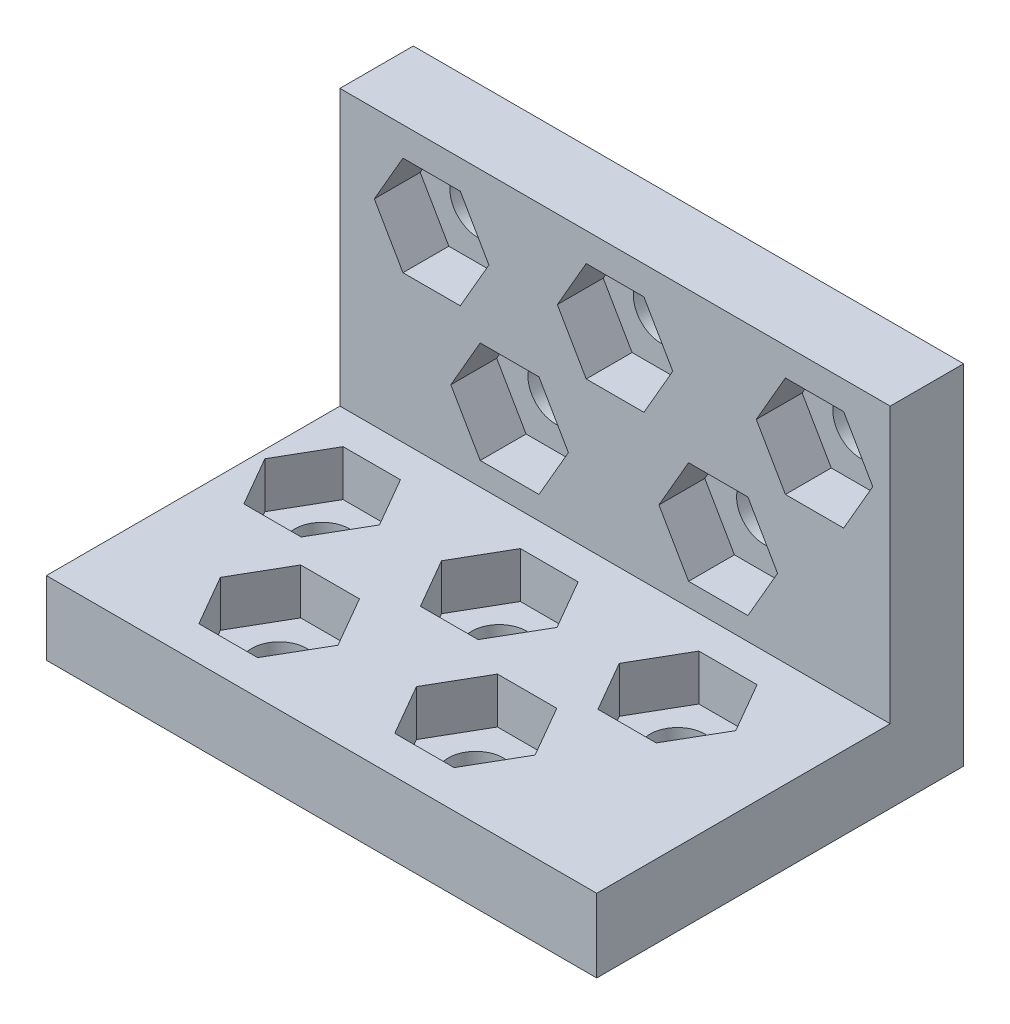
SolidWorks part; units mm, degrees
ref_plane "Front Plane" through (0, 0, 0) normal (0, 0, 1) x (1, 0, 0)
ref_plane "Top Plane" through (0, 0, 0) normal (0, 1, 0) x (1, 0, 0)
ref_plane "Right Plane" through (0, 0, 0) normal (1, 0, 0) x (0, 0, -1)
sketch "Sketch1" plane through (0, 0, 0) normal (0, 1, 0) x (1, 0, 0)
  line L1 (-15, 10) -> (15, 10)
  line L2 (-15, 10) -> (-15, -10)
  line L3 (-15, -10) -> (15, -10)
  line L4 (15, 10) -> (15, -10)
  line L5 (-15, 10) -> (15, -10) construction
  line L6 (-15, -10) -> (15, 10) construction
  point P0 (0, 0)
  dimension "D1" = 30
  dimension "D2" = 20
extrude "Boss-Extrude1" add sketch "Sketch1" along normal blind 4
sketch "Sketch2" plane through (0, 4, 0) normal (0, 1, 0) x (1, 0, 0)
  line L0 (15, -10) -> (15, 10) construction
  line L1 (-15, 10) -> (15, 10)
  line L2 (-15, 10) -> (-15, 6)
  line L3 (-15, 6) -> (15, 6)
  line L4 (15, 10) -> (15, 6)
  dimension "D1" = 4
extrude "Boss-Extrude2" add sketch "Sketch2" along normal blind 15
sketch "Sketch3" plane through (0, 0, -6) normal (0, 0, 1) x (1, 0, 0)
  line L0 (-15, 4) -> (15, 4) construction
  line L1 (-8.4383, 12.0162) -> (-6.8765, 14.7212)
  line L2 (-6.8765, 14.7212) -> (-8.4383, 17.4262)
  line L3 (-8.4383, 17.4262) -> (-11.5617, 17.4262)
  line L4 (-11.5617, 17.4262) -> (-13.1235, 14.7212)
  line L5 (-13.1235, 14.7212) -> (-11.5617, 12.0162)
  line L6 (-11.5617, 12.0162) -> (-8.4383, 12.0162)
  line L31 (-15, 19) -> (-15, 4) construction
  line L51 (1.5733, 11.993) -> (3.1466, 14.718)
  line L52 (3.1466, 14.718) -> (1.5733, 17.443)
  line L53 (1.5733, 17.443) -> (-1.5733, 17.443)
  line L54 (-1.5733, 17.443) -> (-3.1466, 14.718)
  line L55 (-3.1466, 14.718) -> (-1.5733, 11.993)
  line L56 (-1.5733, 11.993) -> (1.5733, 11.993)
  line L57 (12.4612, 11.9712) -> (14.049, 14.7212)
  line L58 (14.049, 14.7212) -> (12.4612, 17.4712)
  line L59 (12.4612, 17.4712) -> (9.2858, 17.4712)
  line L60 (9.2858, 17.4712) -> (7.6981, 14.7212)
  line L61 (7.6981, 14.7212) -> (9.2858, 11.9712)
  line L62 (9.2858, 11.9712) -> (12.4612, 11.9712)
  line L63 (-4.1471, 5.2564) -> (-2.5449, 8.0314)
  line L64 (-2.5449, 8.0314) -> (-4.1471, 10.8064)
  line L65 (-4.1471, 10.8064) -> (-7.3514, 10.8064)
  line L66 (-7.3514, 10.8064) -> (-8.9535, 8.0314)
  line L67 (-8.9535, 8.0314) -> (-7.3514, 5.2564)
  line L68 (-7.3514, 5.2564) -> (-4.1471, 5.2564)
  line L69 (7.2408, 5.2314) -> (8.8574, 8.0314)
  line L70 (8.8574, 8.0314) -> (7.2408, 10.8314)
  line L71 (7.2408, 10.8314) -> (4.0077, 10.8314)
  line L72 (4.0077, 10.8314) -> (2.3911, 8.0314)
  line L73 (2.3911, 8.0314) -> (4.0077, 5.2314)
  line L74 (4.0077, 5.2314) -> (7.2408, 5.2314)
  circle A0 centre (-10, 14.7212) radius 2.705 construction
  circle A1 centre (0, 14.718) radius 2.725 construction
  circle A2 centre (10.8735, 14.7212) radius 2.75 construction
  circle A3 centre (-5.7492, 8.0314) radius 2.775 construction
  circle A4 centre (5.6242, 8.0314) radius 2.8 construction
  dimension "D4" = 5.5
  dimension "D2" = 5
  dimension "D3" = 5.45
  dimension "D1" = 5.41
  dimension "D5" = 5.55
  dimension "D6" = 5.6
extrude "Cut-Extrude1" cut sketch "Sketch3" against normal blind 2.5
sketch "Sketch4" plane through (0, 0, -8.5) normal (0, 0, 1) x (1, 0, 0)
  circle A0 centre (-10, 14.7212) radius 1.5
  circle A1 centre (0, 14.718) radius 1.5
  circle A2 centre (10.8735, 14.7212) radius 1.5
  circle A3 centre (5.6242, 8.0314) radius 1.5
  circle A4 centre (-5.7492, 8.0314) radius 1.5
  dimension "D1" = 3
  dimension "D2" = 3
  dimension "D3" = 3
  dimension "D4" = 3
  dimension "D5" = 3
extrude "Cut-Extrude2" cut sketch "Sketch4" against normal through all both and the other way through all
sketch "Sketch5" plane through (0, 4, 0) normal (0, 1, 0) x (1, 0, 0)
  line L1 (-9.8742, -1.2364) -> (-8.3125, 1.4686)
  line L2 (-8.3125, 1.4686) -> (-9.8742, 4.1736)
  line L3 (-9.8742, 4.1736) -> (-12.9977, 4.1736)
  line L4 (-12.9977, 4.1736) -> (-14.5594, 1.4686)
  line L5 (-14.5594, 1.4686) -> (-12.9977, -1.2364)
  line L6 (-12.9977, -1.2364) -> (-9.8742, -1.2364)
  line L7 (-0.2077, -1.2564) -> (1.3655, 1.4686)
  line L8 (1.3655, 1.4686) -> (-0.2077, 4.1936)
  line L9 (-0.2077, 4.1936) -> (-3.3543, 4.1936)
  line L10 (-3.3543, 4.1936) -> (-4.9276, 1.4686)
  line L11 (-4.9276, 1.4686) -> (-3.3543, -1.2564)
  line L12 (-3.3543, -1.2564) -> (-0.2077, -1.2564)
  line L13 (9.5241, -1.2814) -> (11.1119, 1.4686)
  line L14 (11.1119, 1.4686) -> (9.5241, 4.2186)
  line L15 (9.5241, 4.2186) -> (6.3487, 4.2186)
  line L16 (6.3487, 4.2186) -> (4.761, 1.4686)
  line L17 (4.761, 1.4686) -> (6.3487, -1.2814)
  line L18 (6.3487, -1.2814) -> (9.5241, -1.2814)
  line L19 (-5.3657, -8.118) -> (-3.7635, -5.343)
  line L20 (-3.7635, -5.343) -> (-5.3657, -2.568)
  line L21 (-5.3657, -2.568) -> (-8.57, -2.568)
  line L22 (-8.57, -2.568) -> (-10.1721, -5.343)
  line L23 (-10.1721, -5.343) -> (-8.57, -8.118)
  line L24 (-8.57, -8.118) -> (-5.3657, -8.118)
  line L25 (5.1786, -7.9556) -> (6.7952, -5.1556)
  line L26 (6.7952, -5.1556) -> (5.1786, -2.3556)
  line L27 (5.1786, -2.3556) -> (1.9454, -2.3556)
  line L28 (1.9454, -2.3556) -> (0.3289, -5.1556)
  line L29 (0.3289, -5.1556) -> (1.9454, -7.9556)
  line L30 (1.9454, -7.9556) -> (5.1786, -7.9556)
  circle A0 centre (-11.436, 1.4686) radius 2.705 construction
  circle A1 centre (-1.781, 1.4686) radius 2.725 construction
  circle A2 centre (7.9364, 1.4686) radius 2.75 construction
  circle A3 centre (-6.9678, -5.343) radius 2.775 construction
  circle A4 centre (3.562, -5.1556) radius 2.8 construction
  dimension "D1" = 5.41
  dimension "D2" = 5.45
  dimension "D3" = 5.5
  dimension "D4" = 5.55
  dimension "D5" = 5.6
extrude "Cut-Extrude3" cut sketch "Sketch5" against normal blind 2.5 and the other way through all
sketch "Sketch6" plane through (0, 1.5, 0) normal (0, 1, 0) x (1, 0, 0)
  circle A0 centre (-11.436, 1.4686) radius 1.5
  circle A1 centre (-1.781, 1.4686) radius 1.5
  circle A2 centre (7.9364, 1.4686) radius 1.5
  circle A3 centre (3.562, -5.1556) radius 1.5
  circle A4 centre (-6.9678, -5.343) radius 1.5
  dimension "D1" = 3
  dimension "D2" = 3
  dimension "D3" = 3
  dimension "D4" = 3
  dimension "D5" = 3
extrude "Cut-Extrude4" cut sketch "Sketch6" against normal through all both and the other way through all
